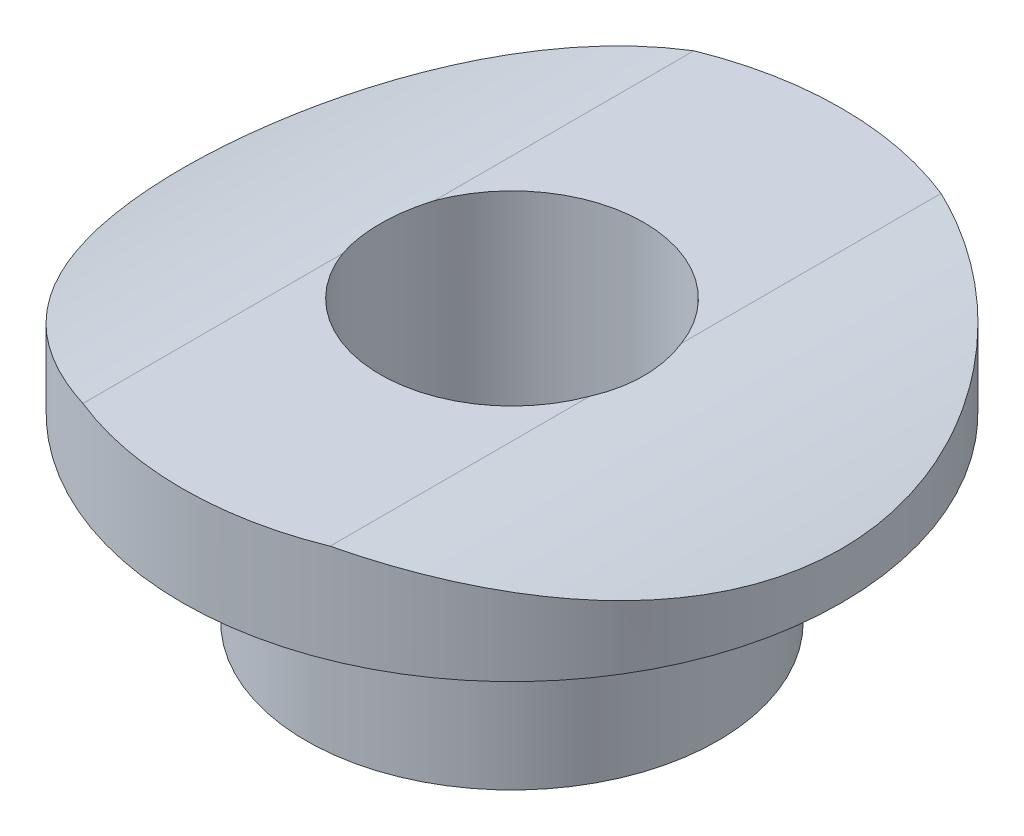
SolidWorks part; units mm, degrees
ref_plane "Front Plane" through (0, 0, 0) normal (0, 0, 1) x (1, 0, 0)
ref_plane "Top Plane" through (0, 0, 0) normal (0, 1, 0) x (1, 0, 0)
ref_plane "Right Plane" through (0, 0, 0) normal (1, 0, 0) x (0, 0, -1)
sketch "Sketch1" plane through (0, 0, 0) normal (0, 0, 1) x (1, 0, 0)
  line L0 (-2.032, 0) -> (-3.175, 0)
  line L1 (-3.175, 0) -> (-3.175, 2.794)
  line L2 (-3.175, 2.794) -> (-5.08, 2.794)
  line L3 (-5.08, 2.794) -> (-5.08, 4.318)
  line L4 (-5.08, 4.318) -> (-2.032, 4.318)
  line L5 (-2.032, 4.318) -> (-2.032, 0)
  dimension "D1" = 3.175
  dimension "D2" = 2.032
  dimension "D3" = 4.318
  dimension "D4" = 1.524
  dimension "D5" = 5.08
ref_axis "Axis1" through (0, 0, 0) along (0, 1, 0)
revolve "Revolve1" add sketch "Sketch1" angle 360 about axis through (0, 0, 0) along (0, 1, 0)
sketch "Sketch3" plane through (0, 0, 0) normal (0, 0, 1) x (1, 0, 0)
  line L0 (0, 0) -> (0, 4.1726) construction
  line L4 (-5.08, 2.794) -> (5.08, 2.794) construction
  circle A0 centre (0, -9.906) radius 12.7 construction
  circle A1 centre (0, -9.906) radius 14.351
  circle A2 centre (0, -9.906) radius 19.05
  dimension "D1" = 25.4
  dimension "D2" = 28.702
  dimension "D3" = 38.1
extrude "Cut-Extrude1" cut sketch "Sketch3" against normal through all and the other way through all contours A2 | A1
